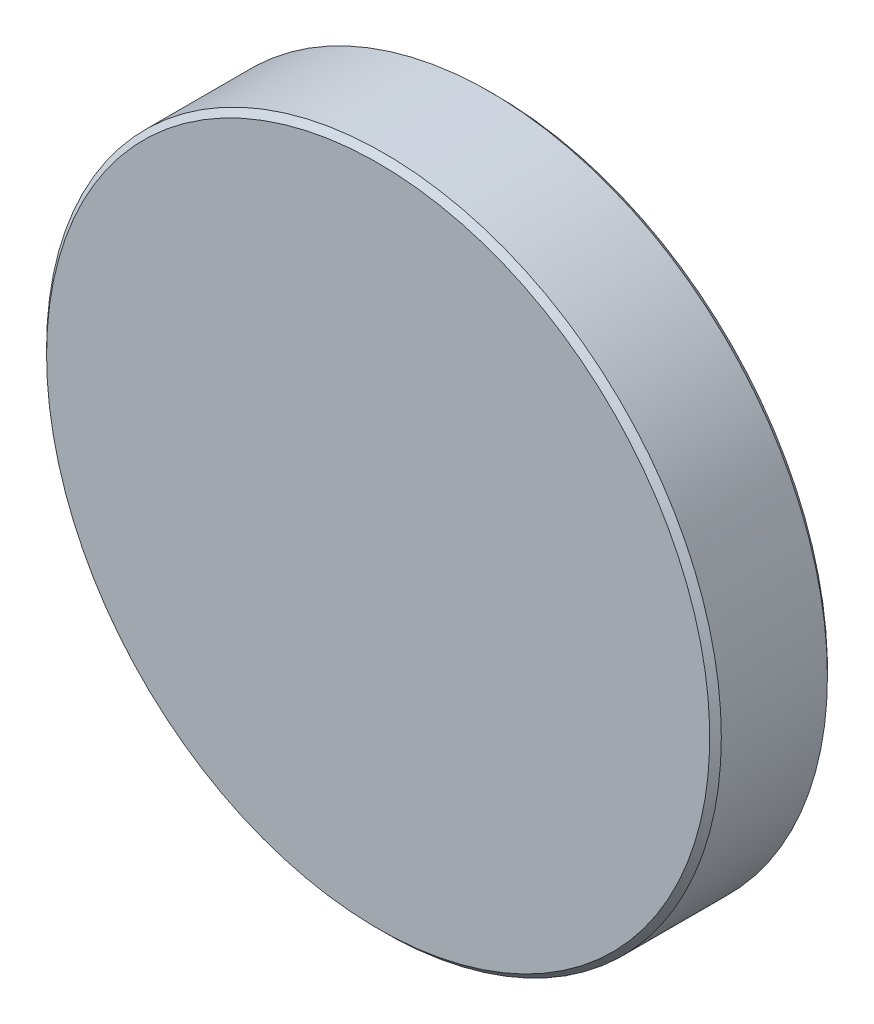
SolidWorks part; units mm, degrees
ref_plane "Front Plane" through (0, 0, 0) normal (0, 0, 1) x (1, 0, 0)
ref_plane "Top Plane" through (0, 0, 0) normal (0, 1, 0) x (1, 0, 0)
ref_plane "Right Plane" through (0, 0, 0) normal (1, 0, 0) x (0, 0, -1)
ref_plane "Plane2" through (0, 0, 0) normal (0, -1, 0) x (-1, 0, 0)
sketch "Sketch5" plane through (0, 0, 0) normal (0, -1, 0) x (-1, 0, 0)
  line L0 (-6.25, -0.2456) -> (0, -0.2456)
  line L1 (0, -0.2456) -> (0, 1.9727)
  line L2 (0, 1.9727) -> (-6.25, 1.9727)
  line L3 (-6.25, 1.9727) -> (-6.3592, 1.8635)
  line L4 (-6.3592, 1.8635) -> (-6.3592, -0.1365)
  line L5 (-6.3592, -0.1365) -> (-6.25, -0.2456)
  line L6 (0, -0.2456) -> (0, 1.9727) construction
  dimension "D1" = 6.25
  dimension "D2" = 2
revolve "Revolve2" add sketch "Sketch5" angle 360 about L6
